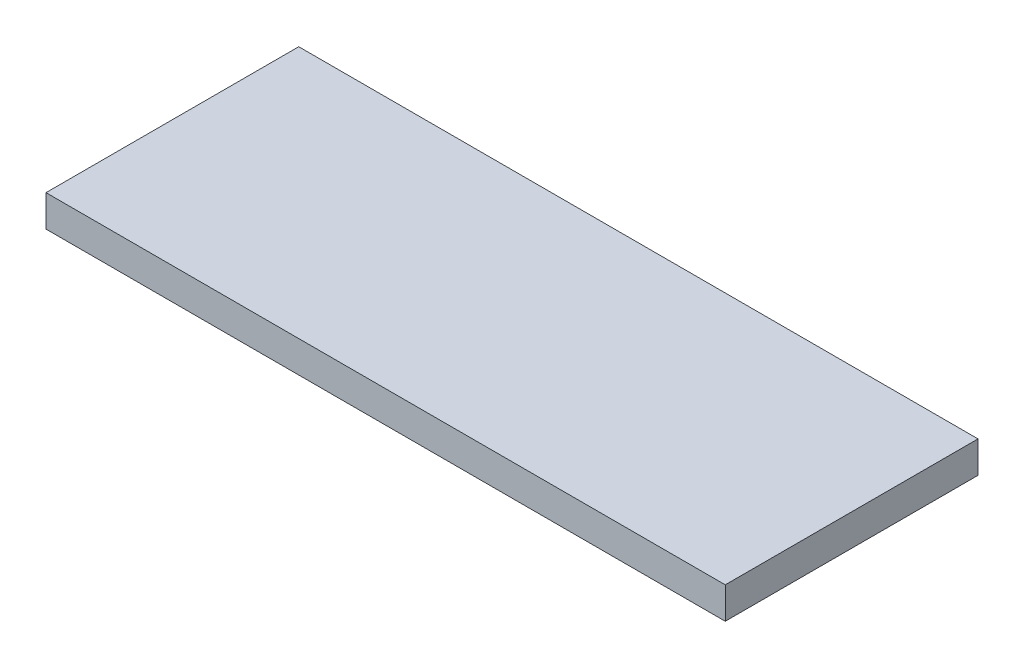
SolidWorks part; units mm, degrees
ref_plane "Alzado" through (0, 0, 0) normal (0, 0, 1) x (1, 0, 0)
ref_plane "Planta" through (0, 0, 0) normal (0, 1, 0) x (1, 0, 0)
ref_plane "Vista lateral" through (0, 0, 0) normal (1, 0, 0) x (0, 0, -1)
sketch "Croquis1" plane through (0, 0, 0) normal (0, 1, 0) x (1, 0, 0)
  line L1 (86, -32) -> (-86, -32)
  line L2 (86, -32) -> (86, 32)
  line L3 (86, 32) -> (-86, 32)
  line L4 (-86, -32) -> (-86, 32)
  line L5 (86, -32) -> (-86, 32) construction
  line L6 (86, 32) -> (-86, -32) construction
  point P0 (0, 0)
  dimension "D1" = 172
  dimension "D2" = 64
extrude "Saliente-Extruir1" add sketch "Croquis1" along normal blind 8
